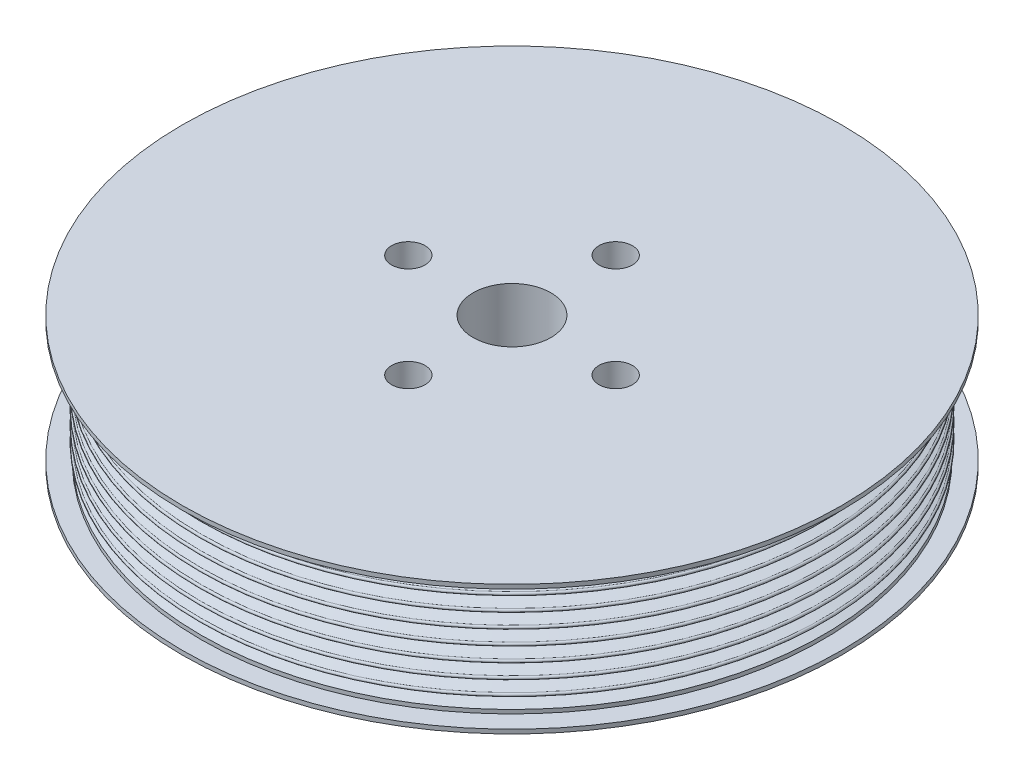
SolidWorks part; units mm, degrees
material "6061-T6 (SS)"
ref_plane "Front Plane" through (0, 0, 0) normal (0, 0, 1) x (1, 0, 0)
ref_plane "Top Plane" through (0, 0, 0) normal (0, 1, 0) x (1, 0, 0)
ref_plane "Right Plane" through (0, 0, 0) normal (1, 0, 0) x (0, 0, -1)
sketch "Sketch1" plane through (0, 0, 0) normal (0, 0, 1) x (1, 0, 0)
  line L0 (76.2, 13.904) -> (76.2, 14.8565)
  line L1 (76.2, -13.904) -> (76.2, -14.8565)
  line L2 (80.772, -15.8725) -> (76.2, -15.8725)
  line L3 (76.2, -13.904) -> (73.3876, -12.8803)
  line L4 (73.3876, -12.8803) -> (73.3876, -12.1183) construction
  line L5 (73.3876, -12.1183) -> (76.2, -11.0947)
  line L6 (76.2, -11.0947) -> (76.2, -10.3327) construction
  line L7 (76.2, -10.3327) -> (73.3876, -9.3091)
  line L8 (73.3876, -9.3091) -> (73.3876, -8.5471) construction
  line L9 (73.3876, -8.5471) -> (76.2, -7.5235)
  line L10 (76.2, -7.5235) -> (76.2, -6.7615) construction
  line L11 (76.2, -6.7615) -> (73.3876, -5.7379)
  line L12 (73.3876, -5.7379) -> (73.3876, -4.9759) construction
  line L13 (73.3876, -4.9759) -> (76.2, -3.9522)
  line L14 (76.2, -3.9522) -> (76.2, -3.1902) construction
  line L15 (76.2, -3.1902) -> (73.3876, -2.1666)
  line L16 (73.3876, -2.1666) -> (73.3876, -1.4046) construction
  line L17 (73.3876, -1.4046) -> (76.2, -0.381)
  line L18 (76.2, -0.381) -> (76.2, 0.381) construction
  line L19 (76.2, 0.381) -> (73.3876, 1.4046)
  line L20 (73.3876, 1.4046) -> (73.3876, 2.1666) construction
  line L21 (73.3876, 2.1666) -> (76.2, 3.1902)
  line L22 (76.2, 3.1902) -> (76.2, 3.9522) construction
  line L23 (76.2, 3.9522) -> (73.3876, 4.9759)
  line L24 (73.3876, 4.9759) -> (73.3876, 5.7379) construction
  line L25 (73.3876, 5.7379) -> (76.2, 6.7615)
  line L26 (76.2, 6.7615) -> (76.2, 7.5235) construction
  line L27 (76.2, 7.5235) -> (73.3876, 8.5471)
  line L28 (73.3876, 8.5471) -> (73.3876, 9.3091) construction
  line L29 (73.3876, 9.3091) -> (76.2, 10.3327)
  line L30 (76.2, 10.3327) -> (76.2, 11.0947) construction
  line L31 (76.2, 11.0947) -> (73.3876, 12.1183)
  line L32 (73.3876, 12.1183) -> (73.3876, 12.8803) construction
  line L33 (73.3876, 12.8803) -> (76.2, 13.904)
  line L34 (76.2, -15.8725) -> (0, -15.8725)
  line L35 (76.2, 15.8725) -> (0, 15.8725)
  line L36 (0, 15.8725) -> (0, -15.8725)
  line L37 (76.2, 10.7137) -> (23.534, 10.7137) construction
  line L38 (76.2, -13.904) -> (76.2, -11.0947) construction
  line L39 (80.772, -15.8725) -> (80.772, -14.8565)
  line L40 (80.772, -14.8565) -> (76.2, -14.8565)
  line L42 (76.2, 15.8725) -> (80.772, 15.8725)
  line L43 (80.772, 15.8725) -> (80.772, 14.8565)
  line L44 (80.772, 14.8565) -> (76.2, 14.8565)
  arc A0 (73.3876, 12.8803) -> (73.3876, 12.1183) centre (73.3876, 12.4993) ccw
  arc A1 (73.3876, 9.3091) -> (73.3876, 8.5471) centre (73.3876, 8.9281) ccw
  arc A2 (73.3876, 5.7379) -> (73.3876, 4.9759) centre (73.3876, 5.3569) ccw
  arc A3 (73.3876, 2.1666) -> (73.3876, 1.4046) centre (73.3876, 1.7856) ccw
  arc A4 (73.3876, -1.4046) -> (73.3876, -2.1666) centre (73.3876, -1.7856) ccw
  arc A5 (73.3876, -4.9759) -> (73.3876, -5.7379) centre (73.3876, -5.3569) ccw
  arc A6 (73.3876, -8.5471) -> (73.3876, -9.3091) centre (73.3876, -8.9281) ccw
  arc A7 (73.3876, -12.1183) -> (73.3876, -12.8803) centre (73.3876, -12.4993) ccw
  arc A8 (76.2, 11.0947) -> (76.2, 10.3327) centre (76.2, 10.7137) cw
  arc A9 (76.2, 7.5235) -> (76.2, 6.7615) centre (76.2, 7.1425) cw
  arc A10 (76.2, 3.1902) -> (76.2, 3.9522) centre (76.2, 3.5712) ccw
  arc A11 (76.2, -0.381) -> (76.2, 0.381) centre (76.2, 0) ccw
  arc A12 (76.2, -3.9522) -> (76.2, -3.1902) centre (76.2, -3.5712) ccw
  arc A13 (76.2, -7.5235) -> (76.2, -6.7615) centre (76.2, -7.1425) ccw
  arc A14 (76.2, -11.0947) -> (76.2, -10.3327) centre (76.2, -10.7137) ccw
  point P1 (0, 0)
  dimension "D9" = 0.9525
  dimension "D5" = 0.381
  dimension "D1" = 20
  dimension "D2" = 20
  dimension "D3" = 3.5712
  dimension "D4" = 76.2
  dimension "D7" = 4.572
  dimension "D8" = 1.016
revolve "Revolve1" add sketch "Sketch1" angle 360 about L36
sketch "Sketch2" plane through (0, 15.8725, 0) normal (0, 1, 0) x (1, 0, 0)
  circle A0 centre (0, 0) radius 9.525
  dimension "D1" = 19.05
extrude "Cut-Extrude1" cut sketch "Sketch2" against normal through all
sketch "Sketch6" plane through (0, 15.8725, 0) normal (0, 1, 0) x (1, 0, 0)
  circle A0 centre (0, 0) radius 43.5154
  circle A1 centre (0, 0) radius 15.875
  circle A2 centre (0, 0) radius 9.525 construction
  dimension "D1" = 6.35
extrude "Cut-Extrude2" [suppressed] cut sketch "Sketch6" against normal offset from surface (1.27 mm away) 30.48
sketch "Sketch8" plane through (0, -15.8725, 0) normal (0, -1, 0) x (1, 0, 0)
  line L0 (0, 0) -> (0, -25.4) construction
  dimension "D1" = 25.4
hole_wizard "5/16 Clearance Hole1" positions "Sketch10" profile "Sketch11" hole size "5/16" standard "Ansi Inch" end condition through all
sketch "Sketch10" plane through (0, -15.8725, 0) normal (0, -1, 0) x (1, 0, 0)
  point P1 (0, -25.4)
sketch "Sketch11" plane through (0, -15.8725, -25.4) normal (1, 0, 0) x (0, 0, -1)
  line L0 (0, 0) -> (0, 31.7449)
  line L1 (0, 31.7449) -> (4.1021, 31.7449)
  line L2 (4.1021, 31.7449) -> (4.1021, 0)
  line L5 (4.1021, 0) -> (0, 0)
  line L11 (0, -6.35) -> (0, 107.95) construction
  dimension "Thru Hole Dia." = 8.2042
  dimension "Thru Hole Depth" = 31.7449
pattern_circular "CirPattern1" count 4 over 360 about axis through (0, 0, 0) along (0, 1, 0) of "5/16 Clearance Hole1"
equation "\"D2@Sketch1\" = \"D1@Sketch1\""
